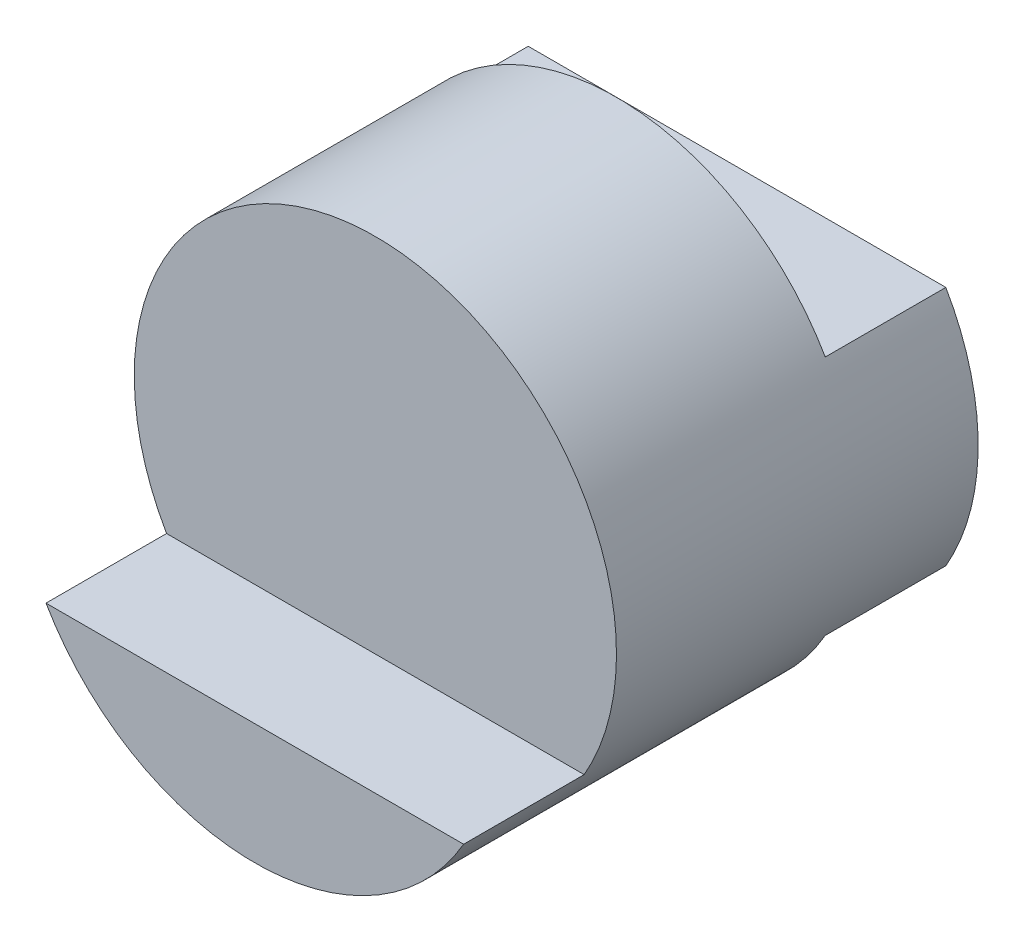
SolidWorks part; units mm, degrees
ref_plane "Front" through (0, 0, 0) normal (0, 0, 1) x (1, 0, 0)
ref_plane "Top" through (0, 0, 0) normal (0, 1, 0) x (1, 0, 0)
ref_plane "Right" through (0, 0, 0) normal (1, 0, 0) x (0, 0, -1)
sketch "Sketch1" plane through (0, 0, 0) normal (0, 0, 1) x (1, 0, 0)
  circle A0 centre (0, 0) radius 2
  dimension "D1" = 4
extrude "Boss-Extrude1" add sketch "Sketch1" along normal blind 3
sketch "Sketch2" plane through (0, 0, 3) normal (0, 0, 1) x (1, 0, 0)
  line L1 (-1.7321, -1) -> (1.7321, -1)
  circle A0 centre (0, 0) radius 2 construction
  arc A2 (-1.7321, -1) -> (1.7321, -1) centre (0, 0) ccw
  dimension "D1" = 1
extrude "Boss-Extrude2" add sketch "Sketch2" along normal blind 1
sketch "Sketch3" plane through (0, 0, 0) normal (0, 0, -1) x (-1, 0, 0)
  line L0 (1.7321, 1) -> (-1.7321, 1)
  arc A0 (1.7321, 1) -> (-1.7321, 1) centre (0, 0) ccw
extrude "Cut-Extrude1" cut sketch "Sketch3" against normal blind 1
sketch "Sketch4" plane through (0, 0, 0) normal (0, 0, -1) x (-1, 0, 0)
  line L0 (1.7321, -1) -> (-1.7321, -1)
  arc A0 (1.7321, -1) -> (-1.7321, -1) centre (0, 0) cw
extrude "Cut-Extrude2" cut sketch "Sketch4" against normal blind 1
